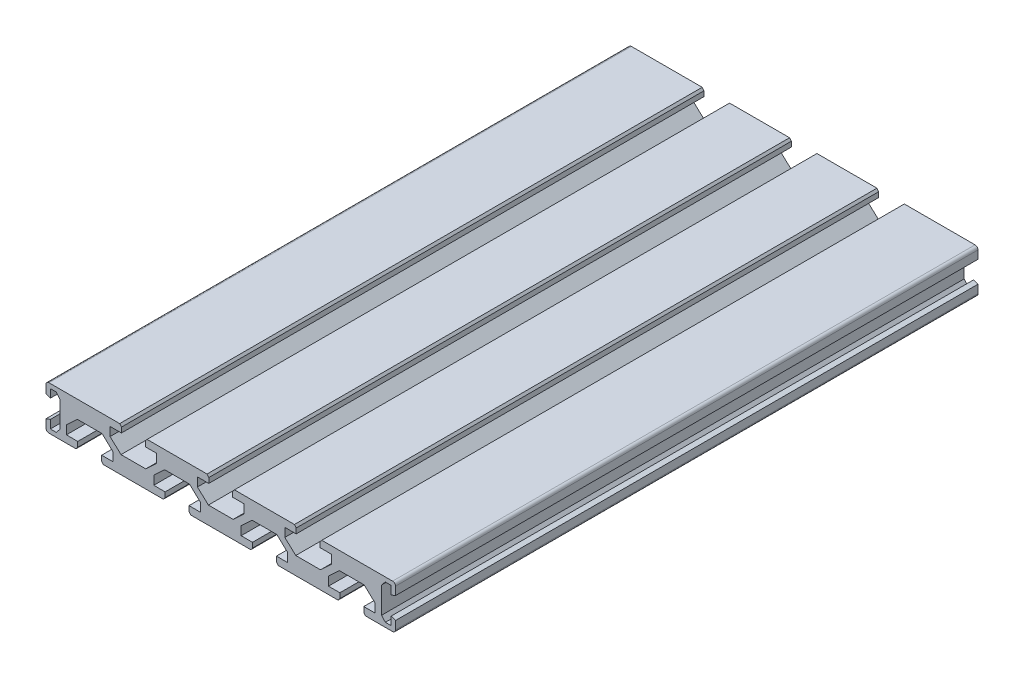
SolidWorks part; units mm, degrees
ref_plane "Ön Düzlem" through (0, 0, 0) normal (0, 0, 1) x (1, 0, 0)
ref_plane "Üst Düzlem" through (0, 0, 0) normal (0, 1, 0) x (1, 0, 0)
ref_plane "Sağ Düzlem" through (0, 0, 0) normal (1, 0, 0) x (0, 0, -1)
sketch "Sketch1" plane through (0, 0, 0) normal (0, 0, 1) x (1, 0, 0)
  line L0 (0, -3.8) -> (120, -3.8) construction
  line L1 (0, 0) -> (120, 0) construction
  line L2 (0, 0) -> (0, -15) construction
  line L3 (0, -15) -> (120, -15) construction
  line L4 (120, 0) -> (120, -15) construction
  line L5 (120, -11.2) -> (0, -11.2) construction
  line L6 (0, -3.8) -> (0, -1)
  line L7 (0, -11.2) -> (0, -14)
  line L8 (60, 0) -> (60, -15) construction
  line L9 (30, 0) -> (30, -15) construction
  line L10 (1, 0) -> (15, 0)
  line L11 (40.3, -15) -> (40.9, -14.25)
  line L12 (40.9, -14.25) -> (40.9, -12.5)
  line L13 (40.9, -12.5) -> (37, -12.5)
  line L14 (37, -12.5) -> (37, -9.5)
  line L15 (37, -9.5) -> (40.75, -6)
  line L16 (40.75, -6) -> (45, -6)
  line L17 (49.25, -6) -> (53, -9.5)
  line L18 (53, -9.5) -> (53, -12.5)
  line L19 (0, -3.8) -> (1.5, -4.35)
  line L20 (1.5, -4.35) -> (1.5, -1.5)
  line L21 (1.5, -1.5) -> (3.5, -1.5)
  line L22 (3.5, -1.5) -> (4.75, -3)
  line L23 (4.75, -3) -> (4.75, -12)
  line L24 (4.75, -12) -> (3.5, -13.5)
  line L25 (3.5, -13.5) -> (1.5, -13.5)
  line L26 (1.5, -13.5) -> (1.5, -10.65)
  line L27 (1.5, -10.65) -> (0, -11.2)
  line L28 (1, -15) -> (10.3, -15)
  line L29 (10.3, -15) -> (10.9, -14.25)
  line L30 (10.9, -14.25) -> (10.9, -12.5)
  line L31 (10.9, -12.5) -> (7, -12.5)
  line L32 (7, -12.5) -> (7, -9.5)
  line L33 (7, -9.5) -> (10.75, -6)
  line L34 (10.75, -6) -> (15, -6)
  line L35 (19.25, -6) -> (23, -9.5)
  line L36 (23, -9.5) -> (23, -12.5)
  line L37 (23, -12.5) -> (19.1, -12.5)
  line L38 (19.1, -12.5) -> (19.1, -14.25)
  line L39 (19.1, -14.25) -> (19.7, -15)
  line L40 (19.7, -15) -> (40.3, -15)
  line L41 (15, -15) -> (15, 0) construction
  line L42 (45, 0) -> (45, -15) construction
  line L43 (75, 0) -> (75, -15) construction
  line L44 (90, 0) -> (90, -15) construction
  line L45 (105, 0) -> (105, -15) construction
  line L46 (15, -6) -> (19.25, -6)
  line L47 (15, 0) -> (23.0206, 0)
  line L48 (53, -12.5) -> (49.1, -12.5)
  line L49 (49.1, -12.5) -> (49.1, -14.25)
  line L50 (49.1, -14.25) -> (49.7, -15)
  line L51 (45, -6) -> (49.25, -6)
  line L52 (70.3, -15) -> (70.9, -14.25)
  line L53 (70.9, -14.25) -> (70.9, -12.5)
  line L54 (70.9, -12.5) -> (67, -12.5)
  line L55 (67, -12.5) -> (67, -9.5)
  line L56 (67, -9.5) -> (70.75, -6)
  line L57 (70.75, -6) -> (75, -6)
  line L58 (79.25, -6) -> (83, -9.5)
  line L59 (83, -9.5) -> (83, -12.5)
  line L60 (83, -12.5) -> (79.1, -12.5)
  line L61 (79.1, -12.5) -> (79.1, -14.25)
  line L62 (79.1, -14.25) -> (79.7, -15)
  line L63 (75, -6) -> (79.25, -6)
  line L64 (100.3, -15) -> (100.9, -14.25)
  line L65 (100.9, -14.25) -> (100.9, -12.5)
  line L66 (100.9, -12.5) -> (97, -12.5)
  line L67 (97, -12.5) -> (97, -9.5)
  line L68 (97, -9.5) -> (100.75, -6)
  line L69 (100.75, -6) -> (105, -6)
  line L70 (109.25, -6) -> (113, -9.5)
  line L71 (113, -9.5) -> (113, -12.5)
  line L72 (113, -12.5) -> (109.1, -12.5)
  line L73 (109.1, -12.5) -> (109.1, -14.25)
  line L74 (109.1, -14.25) -> (109.7, -15)
  line L75 (105, -6) -> (109.25, -6)
  line L76 (49.7, -15) -> (70.3, -15)
  line L77 (79.7, -15) -> (100.3, -15)
  line L78 (109.7, -15) -> (119, -15)
  line L79 (94.7, 0) -> (94.1, -0.75)
  line L80 (55.9, -0.75) -> (55.3, 0)
  line L81 (68, -5.5) -> (64.25, -9)
  line L82 (25.75, -9) -> (22, -5.5)
  line L83 (64.1, -0.75) -> (64.1, -2.5)
  line L84 (85.75, -9) -> (82, -5.5)
  line L85 (52, -2.5) -> (55.9, -2.5)
  line L86 (85.3, 0) -> (64.7, 0)
  line L87 (34.1, -2.5) -> (38, -2.5)
  line L88 (38, -2.5) -> (38, -5.5)
  line L89 (98, -5.5) -> (94.25, -9)
  line L90 (55.3, 0) -> (34.7, 0)
  line L91 (94.1, -2.5) -> (98, -2.5)
  line L92 (64.1, -2.5) -> (68, -2.5)
  line L93 (22, -5.5) -> (22, -2.5)
  line L94 (55.75, -9) -> (52, -5.5)
  line L95 (85.9, -2.5) -> (85.9, -0.75)
  line L96 (25.9, -0.75) -> (25.3, 0)
  line L97 (85.9, -0.75) -> (85.3, 0)
  line L98 (52, -5.5) -> (52, -2.5)
  line L99 (38, -5.5) -> (34.25, -9)
  line L100 (94.25, -9) -> (90, -9)
  line L101 (90, -9) -> (85.75, -9)
  line L102 (64.25, -9) -> (60, -9)
  line L103 (25.9, -2.5) -> (25.9, -0.75)
  line L104 (55.9, -2.5) -> (55.9, -0.75)
  line L105 (98, -2.5) -> (98, -5.5)
  line L106 (64.7, 0) -> (64.1, -0.75)
  line L107 (34.7, 0) -> (34.1, -0.75)
  line L108 (30, -9) -> (25.75, -9)
  line L109 (94.1, -0.75) -> (94.1, -2.5)
  line L110 (60, -9) -> (55.75, -9)
  line L111 (34.25, -9) -> (30, -9)
  line L112 (82, -2.5) -> (85.9, -2.5)
  line L113 (68, -2.5) -> (68, -5.5)
  line L114 (82, -5.5) -> (82, -2.5)
  line L115 (34.1, -0.75) -> (34.1, -2.5)
  line L116 (22, -2.5) -> (25.9, -2.5)
  line L117 (23.0206, 0) -> (25.3, 0)
  line L118 (95.6801, 0) -> (119, 0)
  line L119 (116.5, -13.5) -> (115.25, -12)
  line L120 (120, -11.2) -> (120, -14)
  line L121 (115.25, -12) -> (115.25, -3)
  line L122 (118.5, -1.5) -> (118.5, -4.35)
  line L123 (120, -3.8) -> (120, -1)
  line L124 (115.25, -3) -> (116.5, -1.5)
  line L125 (118.5, -4.35) -> (120, -3.8)
  line L126 (120, -11.2) -> (118.5, -10.65)
  line L127 (116.5, -1.5) -> (118.5, -1.5)
  line L128 (118.5, -10.65) -> (118.5, -13.5)
  line L129 (120, -15) -> (120, 0) construction
  line L130 (118.5, -13.5) -> (116.5, -13.5)
  line L131 (95.6801, 0) -> (94.7, 0)
  arc A0 (119, -15) -> (120, -14) centre (119, -14) ccw
  arc A1 (119, 0) -> (120, -1) centre (119, -1) cw
  arc A2 (0, -1) -> (1, 0) centre (1, -1) cw
  arc A3 (0, -14) -> (1, -15) centre (1, -14) ccw
  point P47 (0, -7.5)
  point P49 (1.5, -13.5)
  point P52 (3.5, -13.5)
  point P53 (45, -6)
  point P55 (4.75, -12)
  point P58 (4.75, -3)
  point P61 (1.5, -1.5)
  point P64 (3.5, -1.5)
  point P67 (1.5, -10.65)
  point P72 (75, -6)
  point P76 (1.5, -4.35)
  point P79 (15, -6)
  point P97 (105, -6)
  point P109 (90, -9)
  point P123 (60, -9)
  point P137 (30, -9)
  point P152 (120, -7.5)
  dimension "D20" = 39.806
  dimension "D39" = 1
  dimension "D1" = 120
  dimension "D2" = 15
  dimension "D3" = 60
  dimension "D4" = 30
  dimension "D5" = 7.4
  dimension "D6" = 3.8
  dimension "D7" = 15
  dimension "D8" = 9.4
  dimension "D9" = 6.3
  dimension "D10" = 0.55
  dimension "D11" = 1.5
  dimension "D12" = 4.7
  dimension "D13" = 2.5
  dimension "D14" = 1.5
  dimension "D15" = 1.5
  dimension "D16" = 4.75
  dimension "D17" = 2
  dimension "D18" = 2
  dimension "D19" = 9
  dimension "D21" = 18
  dimension "D22" = 8
  dimension "D23" = 8
  dimension "D24" = 2.5
  dimension "D25" = 3
  dimension "D26" = 3
  dimension "D27" = 8.5
  dimension "D28" = 1.75
  dimension "D29" = 1.75
  dimension "D30" = 4.1
  dimension "D31" = 4.1
  dimension "D32" = 15
  dimension "D33" = 30
  dimension "D34" = 15
  dimension "D35" = 15
  dimension "D36" = 4.25
  dimension "D37" = 4
  dimension "D38" = 4.75
extrude "Boss-Extrude1" add sketch "Sketch1" against normal blind 200
